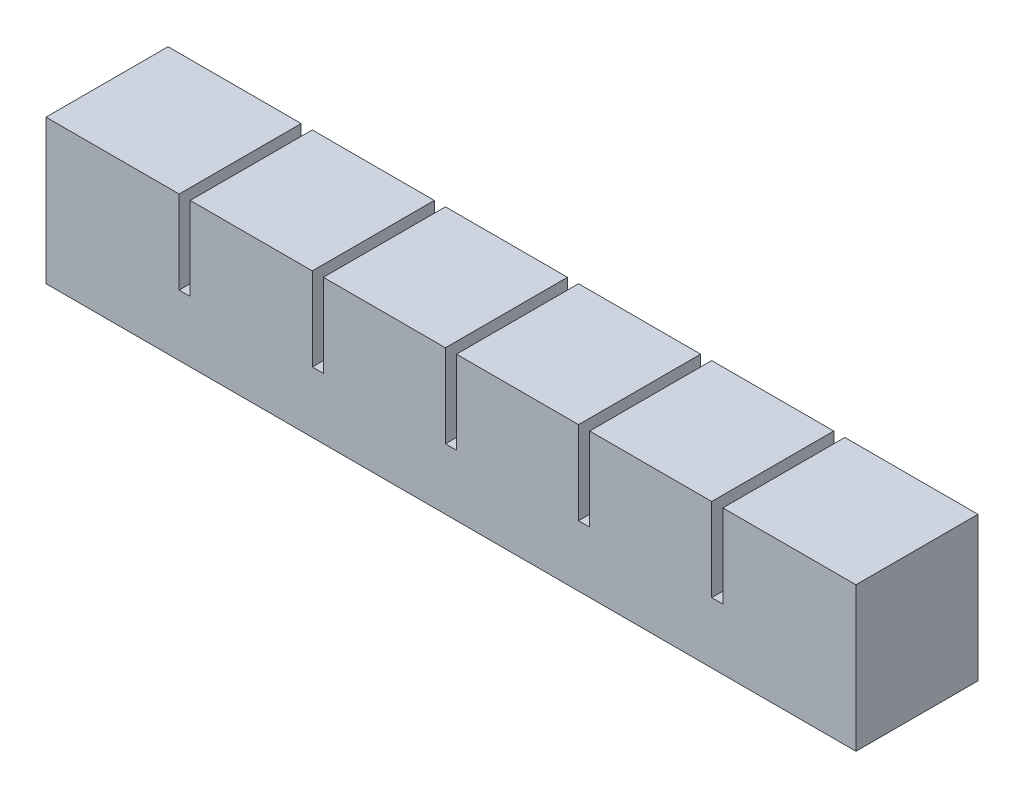
SolidWorks part; units mm, degrees
ref_plane "Front Plane" through (0, 0, 0) normal (0, 0, 1) x (1, 0, 0)
ref_plane "Top Plane" through (0, 0, 0) normal (0, 1, 0) x (1, 0, 0)
ref_plane "Right Plane" through (0, 0, 0) normal (1, 0, 0) x (0, 0, -1)
sketch "Sketch1" plane through (0, 0, 0) normal (0, 0, 1) x (1, 0, 0)
  line L1 (0, 0) -> (22, 0)
  line L2 (0, 0) -> (0, 20)
  line L3 (0, 20) -> (22, 20)
  line L4 (22, 0) -> (22, 20)
  dimension "D1" = 22
  dimension "D2" = 20
extrude "Boss-Extrude1" add sketch "Sketch1" along normal blind 22
sketch "Sketch2" plane through (0, 0, 0) normal (0, -1, 0) x (1, 0, 0)
  line L0 (22, 22) -> (22, 0) construction
  line L1 (5, 17) -> (17, 17)
  line L2 (5, 17) -> (5, 5)
  line L3 (5, 5) -> (17, 5)
  line L4 (17, 17) -> (17, 5)
  line L5 (0, 22) -> (22, 22) construction
  line L6 (0, 22) -> (0, 0) construction
  line L7 (0, 0) -> (22, 0) construction
  dimension "D1" = 5
  dimension "D2" = 5
  dimension "D3" = 5
  dimension "D4" = 5
extrude "Cut-Extrude1" cut sketch "Sketch2" against normal blind 15
sketch "Sketch3" plane through (22, 0, 0) normal (1, 0, 0) x (0, 0, -1)
  line L0 (0, 0) -> (0, 20) construction
  line L1 (-22, 0) -> (0, 0)
  line L2 (-22, 0) -> (-22, 5)
  line L3 (-22, 5) -> (0, 5)
  line L4 (0, 0) -> (0, 5)
  dimension "D1" = 5
extrude "Boss-Extrude2" add sketch "Sketch3" along normal blind 2
pattern_linear "LPattern1" count 6 spacing 24 along (1, 0, 0) of bodies 103
combine bodies "Combine1" operation type add bodies to combine 105 106 107 108 104 103
sketch "Sketch4" plane through (142, 0, 0) normal (1, 0, 0) x (0, 0, -1)
  line L1 (-22, 5) -> (0, 5)
  line L2 (-22, 5) -> (-22, 20)
  line L3 (-22, 20) -> (0, 20)
  line L4 (0, 5) -> (0, 20)
extrude "Boss-Extrude3" add sketch "Sketch4" along normal up to surface (2 mm away) up to face at (144, 2.5, 11)
sketch "Sketch5" plane through (0, 0, 0) normal (-1, 0, 0) x (0, 0, 1)
  line L1 (22, 0) -> (0, 0)
  line L2 (22, 0) -> (22, 20)
  line L3 (22, 20) -> (0, 20)
  line L4 (0, 0) -> (0, 20)
extrude "Boss-Extrude4" add sketch "Sketch5" along normal blind 2
ref_point "Point1"
sketch "Sketch6" plane through (0, 0, 0) normal (0, -1, 0) x (-1, 0, 0)
  line L0 (-137, -5) -> (-137, -17) construction
  line L1 (-5, -10) -> (-137, -10)
  line L2 (-5, -10) -> (-5, -12)
  line L3 (-5, -12) -> (-137, -12)
  line L4 (-137, -10) -> (-137, -12)
  line L5 (-5, -10) -> (-137, -12) construction
  line L6 (-5, -12) -> (-137, -10) construction
  point P0 (-71, -11)
  dimension "D1" = 2
extrude "Cut-Extrude2" cut sketch "Sketch6" against normal blind 2
sketch "Sketch7" plane through (0, 0, 0) normal (0, -1, 0) x (-1, 0, 0)
  line L1 (2, -22) -> (-144, -22)
  line L2 (2, -22) -> (2, 0)
  line L3 (2, 0) -> (-144, 0)
  line L4 (-144, -22) -> (-144, 0)
extrude "Boss-Extrude5" add sketch "Sketch7" along normal blind 6
